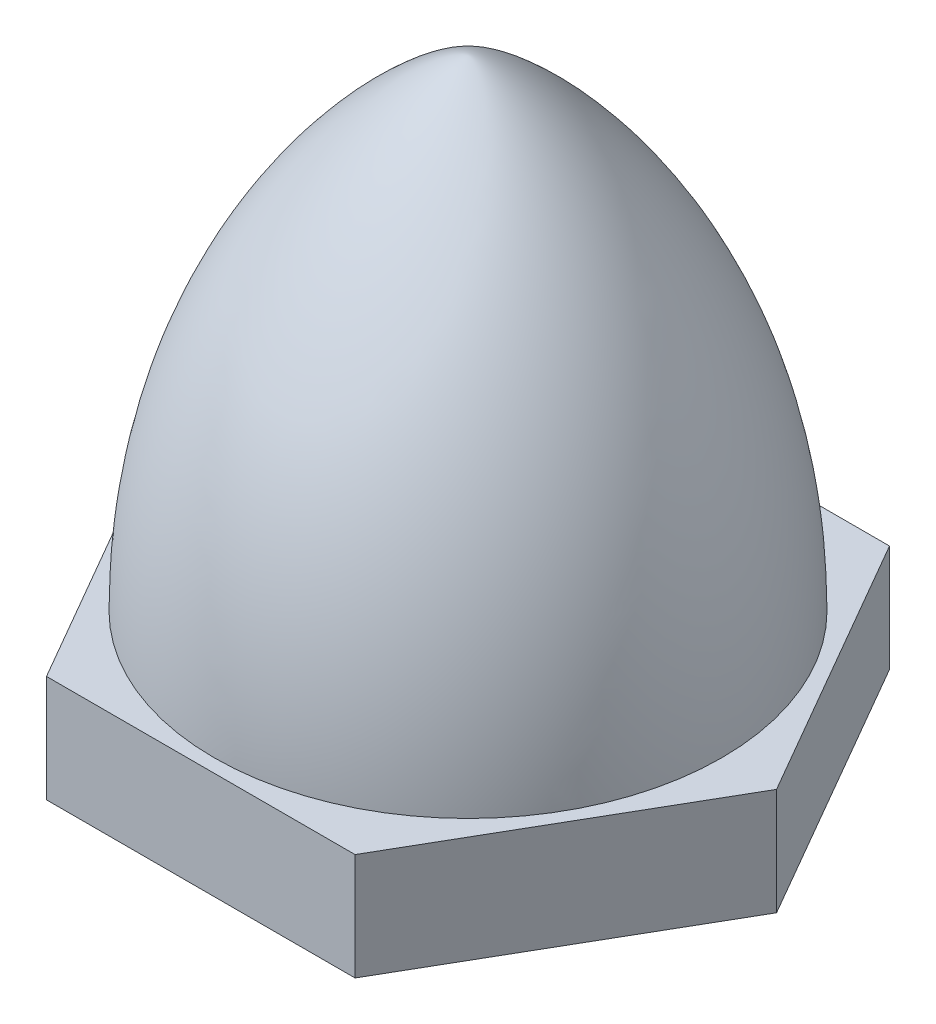
SolidWorks part; units mm, degrees
ref_plane "Front Plane" through (0, 0, 0) normal (0, 0, 1) x (1, 0, 0)
ref_plane "Top Plane" through (0, 0, 0) normal (0, 1, 0) x (1, 0, 0)
ref_plane "Right Plane" through (0, 0, 0) normal (1, 0, 0) x (0, 0, -1)
sketch "Sketch1" plane through (0, 0, 0) normal (0, 1, 0) x (1, 0, 0)
  line L0 (0, 0) -> (2.1052, 0) construction
  line L1 (2.8868, 5) -> (-2.8868, 5)
  line L2 (-2.8868, 5) -> (-5.7735, 0)
  line L3 (-5.7735, 0) -> (-2.8868, -5)
  line L4 (-2.8868, -5) -> (2.8868, -5)
  line L5 (2.8868, -5) -> (5.7735, 0)
  line L6 (5.7735, 0) -> (2.8868, 5)
  circle A0 centre (0, 0) radius 5 construction
  dimension "D1" = 10
extrude "Boss-Extrude1" add sketch "Sketch1" along normal blind 2
sketch "Sketch2" plane through (0, 0, 0) normal (0, 0, 1) x (1, 0, 0)
  line L0 (0, 0) -> (0, 11) construction
  line L1 (5.7735, 2) -> (2.8868, 2) construction
  line L2 (4.0706, 11) -> (-4.0706, 11) construction
  line L3 (4.75, -2.8034) -> (4.75, 6.8034) construction
  line L4 (4.75, 2) -> (0, 2)
  line L5 (0, 11) -> (0, 2)
  spline S0 degree 3 poles (0, 11) (0.6225, 11) (4.75, 8.0042) (4.75, 2) knots 0 0 0 0 1 1 1 1
  dimension "D1" = 11
  dimension "D2" = 4.75
revolve "Revolve1" add sketch "Sketch2" angle 360 about L5
hole_wizard "M5x0.8 Tapped Hole1" positions "Sketch5" profile "Sketch4" tap size "M5x0.8" standard "BSI"
sketch "Sketch5" plane through (0, 0, 0) normal (0, -1, 0) x (-1, 0, 0)
  point P0 (0, 0)
sketch "Sketch4" plane through (0, 0, 0) normal (1, 0, 0) x (0, 0, -1)
  line L0 (0, 0) -> (0, 6.2618)
  line L1 (0, 6.2618) -> (2.1, 5)
  line L2 (2.1, 5) -> (2.1, 0)
  line L5 (2.1, 0) -> (0, 0)
  line L10 (0, 6.2618) -> (-2.1, 5) construction
  line L11 (0, -6.35) -> (0, 107.95) construction
  dimension "Tap Drill Dia." = 4.2
  dimension "Tap Drill Depth" = 5
  dimension "Drill Angle" = 118
cosmetic thread "Hole Thread1" parameters "D1"=5, "D2"=5
